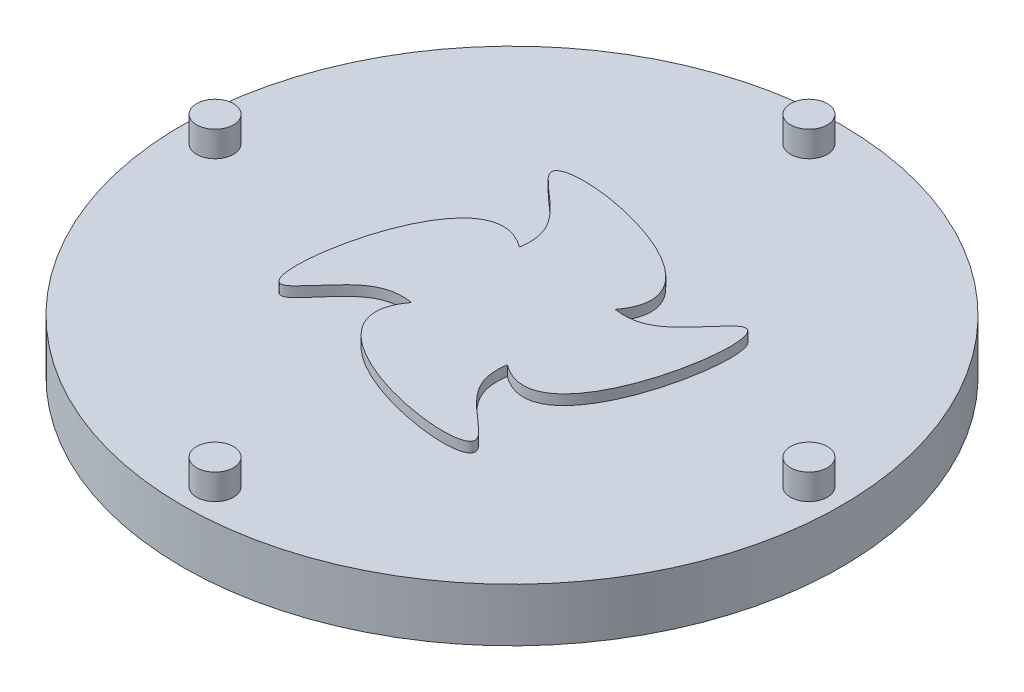
SolidWorks part; units mm, degrees
ref_plane "Alzado" through (0, 0, 0) normal (0, 0, 1) x (1, 0, 0)
ref_plane "Planta" through (0, 0, 0) normal (0, 1, 0) x (1, 0, 0)
ref_plane "Vista lateral" through (0, 0, 0) normal (1, 0, 0) x (0, 0, -1)
sketch "Croquis1" plane through (0, 0, 0) normal (0, 1, 0) x (1, 0, 0)
  circle A0 centre (0, 0) radius 61.815
  dimension "D1" = 123.63
extrude "Saliente-Extruir1" add sketch "Croquis1" along normal blind 10
sketch "Croquis2" plane through (0, 10, 0) normal (0, 1, 0) x (1, 0, 0)
  circle A0 centre (0, 55.6983) radius 3.45
  circle A1 centre (55.6983, 0) radius 3.45
  circle A2 centre (0, -55.6983) radius 3.45
  circle A3 centre (-55.6983, 0) radius 3.45
  point P12 (0, 0)
  dimension "D1" = 6.9
  dimension "D2" = 55.6983
  dimension "D3" = 4
extrude "Saliente-Extruir2" add sketch "Croquis2" along normal blind 4.8
sketch "Croquis3" plane through (0, 10, 0) normal (0, 1, 0) x (1, 0, 0)
  arc A0 (-8.7616, -8.3397) -> (-7.4839, -9.6174) centre (0.693, -0.1628) ccw
  spline S0 degree 3 poles (-9.4181, 8.8286) (-14.2169, 15.2422) (-2.4097, 26.5738) (27.3699, 28.459) (10.0048, 18.1784) (9.3364, 12.083) (9.6844, 9.9482) knots 0.00619 0.00619 0.00619 0.00619 0.153841 0.345958 0.455748 0.513421 0.513421 0.513421 0.513421
  spline S1 degree 3 poles (9.6844, 9.9482) (16.098, 14.7471) (27.4296, 2.9398) (29.3148, -26.8397) (19.0342, -9.4746) (12.9388, -8.8062) (10.804, -9.1542) knots 0.00619 0.00619 0.00619 0.00619 0.153841 0.345958 0.455748 0.513421 0.513421 0.513421 0.513421
  spline S2 degree 3 poles (10.804, -9.1542) (15.6028, -15.5678) (3.7956, -26.8994) (-25.9839, -28.7846) (-8.6188, -18.5041) (-7.9504, -12.4086) (-8.2984, -10.2739) knots 0.00619 0.00619 0.00619 0.00619 0.153841 0.345958 0.455748 0.513421 0.513421 0.513421 0.513421
  spline S3 degree 3 poles (-8.2984, -10.2739) (-14.712, -15.0727) (-26.0436, -3.2655) (-27.9289, 26.5141) (-17.6483, 9.149) (-11.5528, 8.4806) (-9.4181, 8.8286) knots 0.00619 0.00619 0.00619 0.00619 0.153841 0.345958 0.455748 0.513421 0.513421 0.513421 0.513421
  point P19 (0.693, -0.1628)
  dimension "D1" = 25
sketch "Croquis4" plane through (0, 0, 0) normal (0, -1, 0) x (1, 0, 0)
  spline S0 degree 3 poles (-9.5856, 9.2541) (-14.3844, 15.6677) (-2.5772, 26.9994) (27.2024, 28.8846) (9.8372, 18.604) (9.1688, 12.5086) (9.5168, 10.3738) knots 0.00619 0.00619 0.00619 0.00619 0.153841 0.345958 0.455748 0.513421 0.513421 0.513421 0.513421
  spline S1 degree 3 poles (9.5168, 10.3738) (15.9305, 15.1726) (27.2621, 3.3654) (29.1473, -26.4142) (18.8667, -9.049) (12.7713, -8.3807) (10.6365, -8.7286) knots 0.00619 0.00619 0.00619 0.00619 0.153841 0.345958 0.455748 0.513421 0.513421 0.513421 0.513421
  spline S2 degree 3 poles (10.6365, -8.7286) (15.4353, -15.1423) (3.6281, -26.4739) (-26.1514, -28.3591) (-8.7863, -18.0785) (-8.1179, -11.9831) (-8.4659, -9.8483) knots 0.00619 0.00619 0.00619 0.00619 0.153841 0.345958 0.455748 0.513421 0.513421 0.513421 0.513421
  spline S3 degree 3 poles (-8.4659, -9.8483) (-14.8795, -14.6471) (-26.2112, -2.8399) (-28.0964, 26.9396) (-17.8158, 9.5745) (-11.7204, 8.9061) (-9.5856, 9.2541) knots 0.00619 0.00619 0.00619 0.00619 0.153841 0.345958 0.455748 0.513421 0.513421 0.513421 0.513421
extrude "Saliente-Extruir5" add sketch "Croquis4" against normal blind 11.9
sketch "Croquis5" plane through (0, 0, 0) normal (0, -1, 0) x (1, 0, 0)
  line L0 (0, -967.0228) -> (0, -35.5) construction
  line L1 (-2.8962, 35.3817) -> (-2.8962, 36.3478)
  line L2 (12.1702, 43.8511) -> (10.4606, 44.29)
  line L3 (0.8825, 45.5) -> (-0.8825, 45.5)
  line L4 (2.8962, 35.3817) -> (2.8962, 36.3478)
  line L5 (22.6931, 39.4468) -> (21.1464, 40.2971)
  line L6 (31.7902, 32.564) -> (30.5036, 33.7722)
  line L7 (38.8898, 23.635) -> (37.9441, 25.1252)
  line L8 (43.5458, 13.221) -> (43.0004, 14.8996)
  line L9 (45.4656, 1.9762) -> (45.3548, 3.7377)
  line L10 (44.5287, -9.3927) -> (44.8594, -7.659)
  line L11 (40.7939, -20.1715) -> (41.5454, -18.5744)
  line L12 (34.4958, -29.6828) -> (35.6209, -28.3228)
  line L13 (26.0303, -37.329) -> (27.4582, -36.2915)
  line L14 (15.9291, -42.6297) -> (17.5702, -41.98)
  line L15 (4.8271, -45.2518) -> (6.5782, -45.0306)
  line L16 (-6.5782, -45.0306) -> (-4.8271, -45.2518)
  line L17 (-17.5702, -41.98) -> (-15.9291, -42.6297)
  line L18 (-27.4582, -36.2915) -> (-26.0303, -37.329)
  line L19 (-35.6209, -28.3228) -> (-34.4958, -29.6828)
  line L20 (-41.5454, -18.5744) -> (-40.7939, -20.1715)
  line L21 (-44.8594, -7.659) -> (-44.5287, -9.3927)
  line L22 (-45.3548, 3.7377) -> (-45.4656, 1.9762)
  line L23 (-43.0004, 14.8996) -> (-43.5458, 13.221)
  line L24 (-37.9441, 25.1252) -> (-38.8898, 23.635)
  line L25 (-30.5036, 33.7722) -> (-31.7902, 32.564)
  line L26 (-21.1464, 40.2971) -> (-22.6931, 39.4468)
  line L27 (-10.4606, 44.29) -> (-12.1702, 43.8511)
  line L28 (5.9939, 34.9903) -> (6.2341, 35.9262)
  line L29 (11.6043, 33.5498) -> (11.8445, 34.4857)
  line L30 (14.5073, 32.4004) -> (14.9728, 33.2471)
  line L31 (19.5832, 29.6099) -> (20.0487, 30.4566)
  line L32 (22.1092, 27.7747) -> (22.7706, 28.479)
  line L33 (26.3316, 23.8095) -> (26.993, 24.5139)
  line L34 (28.3219, 21.4038) -> (29.1376, 21.9215)
  line L35 (31.4256, 16.5131) -> (32.2414, 17.0308)
  line L36 (32.755, 13.688) -> (33.6739, 13.9865)
  line L37 (34.5449, 8.1791) -> (35.4638, 8.4777)
  line L38 (35.13, 5.1121) -> (36.0943, 5.1728)
  line L39 (35.4937, -0.6688) -> (36.458, -0.6082)
  line L40 (35.2976, -3.785) -> (36.2467, -3.966)
  line L41 (34.2123, -9.4748) -> (35.1613, -9.6558)
  line L42 (33.2474, -12.4442) -> (34.1217, -12.8556)
  line L43 (30.7811, -17.6853) -> (31.6554, -18.0967)
  line L44 (29.1081, -20.3216) -> (29.8526, -20.9374)
  line L45 (25.4159, -24.7847) -> (26.1604, -25.4005)
  line L46 (23.1399, -26.922) -> (23.7078, -27.7037)
  line L47 (18.4538, -30.3267) -> (19.0217, -31.1084)
  line L48 (15.7177, -31.8309) -> (16.0733, -32.7292)
  line L49 (10.3321, -33.9632) -> (10.6877, -34.8615)
  line L50 (7.3078, -34.7397) -> (7.4289, -35.6982)
  line L51 (1.5611, -35.4657) -> (1.6822, -36.4242)
  line L52 (-1.5611, -35.4657) -> (-1.6822, -36.4242)
  line L53 (-7.3078, -34.7397) -> (-7.4289, -35.6982)
  line L54 (-10.3321, -33.9632) -> (-10.6877, -34.8615)
  line L55 (-15.7177, -31.8309) -> (-16.0733, -32.7292)
  line L56 (-18.4538, -30.3267) -> (-19.0217, -31.1084)
  line L57 (-23.1399, -26.922) -> (-23.7078, -27.7037)
  line L58 (-25.4159, -24.7847) -> (-26.1604, -25.4005)
  line L59 (-29.1081, -20.3216) -> (-29.8526, -20.9374)
  line L60 (-30.7811, -17.6853) -> (-31.6554, -18.0967)
  line L61 (-33.2474, -12.4442) -> (-34.1217, -12.8556)
  line L62 (-34.2123, -9.4748) -> (-35.1613, -9.6558)
  line L63 (-35.2976, -3.785) -> (-36.2467, -3.966)
  line L64 (-35.4937, -0.6688) -> (-36.458, -0.6082)
  line L65 (-35.13, 5.1121) -> (-36.0943, 5.1728)
  line L66 (-34.5449, 8.1791) -> (-35.4638, 8.4777)
  line L67 (-32.755, 13.688) -> (-33.6739, 13.9865)
  line L68 (-31.4256, 16.5131) -> (-32.2414, 17.0308)
  line L69 (-28.3219, 21.4038) -> (-29.1376, 21.9215)
  line L70 (-26.3316, 23.8095) -> (-26.993, 24.5139)
  line L71 (-22.1092, 27.7747) -> (-22.7706, 28.479)
  line L72 (-19.5832, 29.6099) -> (-20.0487, 30.4566)
  line L73 (-14.5073, 32.4004) -> (-14.9728, 33.2471)
  line L74 (-11.6043, 33.5498) -> (-11.8445, 34.4857)
  line L75 (-5.9939, 34.9903) -> (-6.2341, 35.9262)
  arc A0 (-2.8962, 35.3817) -> (-5.9939, 34.9903) centre (0, 0) ccw
  arc A1 (-2.8962, 36.3478) -> (-0.8825, 45.5) centre (18.9088, 36.3478) cw
  arc A2 (2.8962, 36.3478) -> (0.8825, 45.5) centre (-18.9088, 36.3478) ccw
  arc A3 (6.2341, 35.9262) -> (10.4606, 44.29) centre (27.3541, 30.5035) cw
  arc A4 (14.9728, 33.2471) -> (21.1464, 40.2971) centre (34.0806, 22.7425) cw
  arc A5 (22.7706, 28.479) -> (30.5036, 33.7722) centre (38.6658, 13.5524) cw
  arc A6 (29.1376, 21.9215) -> (37.9441, 25.1252) centre (40.8214, 3.5109) cw
  arc A7 (33.6739, 13.9865) -> (43.0004, 14.8996) centre (40.412, -6.7513) cw
  arc A8 (36.0943, 5.1728) -> (45.3548, 3.7377) centre (37.4634, -16.5892) cw
  arc A9 (36.2467, -3.966) -> (44.8594, -7.659) centre (32.1609, -25.3848) cw
  arc A10 (34.1217, -12.8556) -> (41.5454, -18.5744) centre (24.8375, -32.5854) cw
  arc A11 (29.8526, -20.9374) -> (35.6209, -28.3228) centre (15.9535, -37.7385) cw
  arc A12 (23.7078, -27.7037) -> (27.4582, -36.2915) centre (6.0672, -40.5204) cw
  arc A13 (16.0733, -32.7292) -> (17.5702, -41.98) centre (-4.2005, -40.7562) cw
  arc A14 (7.4289, -35.6982) -> (6.5782, -45.0306) centre (-14.2041, -38.4311) cw
  arc A15 (-1.6822, -36.4242) -> (-4.8271, -45.2518) centre (-23.3153, -33.6913) cw
  arc A16 (-10.6877, -34.8615) -> (-15.9291, -42.6297) centre (-30.9615, -26.8346) cw
  arc A17 (-19.0217, -31.1084) -> (-26.0303, -37.329) centre (-36.6623, -18.2917) cw
  arc A18 (-26.1604, -25.4005) -> (-34.4958, -29.6828) centre (-40.0594, -8.5995) cw
  arc A19 (-31.6554, -18.0967) -> (-40.7939, -20.1715) centre (-40.9395, 1.6331) cw
  arc A20 (-35.1613, -9.6558) -> (-44.5287, -9.3927) centre (-39.2472, 11.763) cw
  arc A21 (-36.458, -0.6082) -> (-45.4656, 1.9762) centre (-35.0888, 21.1538) cw
  arc A22 (-35.4638, 8.4777) -> (-43.5458, 13.221) centre (-28.7257, 29.2155) cw
  arc A23 (-32.2414, 17.0308) -> (-38.8898, 23.635) centre (-20.5576, 35.4414) cw
  arc A24 (-26.993, 24.5139) -> (-31.7902, 32.564) centre (-11.0979, 39.4404) cw
  arc A25 (-20.0487, 30.4566) -> (-22.6931, 39.4468) centre (-0.9408, 40.9613) cw
  arc A26 (-11.8445, 34.4857) -> (-12.1702, 43.8511) centre (9.2754, 39.9083) cw
  arc A27 (11.8445, 34.4857) -> (12.1702, 43.8511) centre (-9.2754, 39.9083) ccw
  arc A28 (20.0487, 30.4566) -> (22.6931, 39.4468) centre (0.9408, 40.9613) ccw
  arc A29 (26.993, 24.5139) -> (31.7902, 32.564) centre (11.0979, 39.4404) ccw
  arc A30 (32.2414, 17.0308) -> (38.8898, 23.635) centre (20.5576, 35.4414) ccw
  arc A31 (35.4638, 8.4777) -> (43.5458, 13.221) centre (28.7257, 29.2155) ccw
  arc A32 (36.458, -0.6082) -> (45.4656, 1.9762) centre (35.0888, 21.1538) ccw
  arc A33 (35.1613, -9.6558) -> (44.5287, -9.3927) centre (39.2472, 11.763) ccw
  arc A34 (31.6554, -18.0967) -> (40.7939, -20.1715) centre (40.9395, 1.6331) ccw
  arc A35 (26.1604, -25.4005) -> (34.4958, -29.6828) centre (40.0594, -8.5995) ccw
  arc A36 (19.0217, -31.1084) -> (26.0303, -37.329) centre (36.6623, -18.2917) ccw
  arc A37 (10.6877, -34.8615) -> (15.9291, -42.6297) centre (30.9615, -26.8346) ccw
  arc A38 (1.6822, -36.4242) -> (4.8271, -45.2518) centre (23.3153, -33.6913) ccw
  arc A39 (-7.4289, -35.6982) -> (-6.5782, -45.0306) centre (14.2041, -38.4311) ccw
  arc A40 (-16.0733, -32.7292) -> (-17.5702, -41.98) centre (4.2005, -40.7562) ccw
  arc A41 (-23.7078, -27.7037) -> (-27.4582, -36.2915) centre (-6.0672, -40.5204) ccw
  arc A42 (-29.8526, -20.9374) -> (-35.6209, -28.3228) centre (-15.9535, -37.7385) ccw
  arc A43 (-34.1217, -12.8556) -> (-41.5454, -18.5744) centre (-24.8375, -32.5854) ccw
  arc A44 (-36.2467, -3.966) -> (-44.8594, -7.659) centre (-32.1609, -25.3848) ccw
  arc A45 (-36.0943, 5.1728) -> (-45.3548, 3.7377) centre (-37.4634, -16.5892) ccw
  arc A46 (-33.6739, 13.9865) -> (-43.0004, 14.8996) centre (-40.412, -6.7513) ccw
  arc A47 (-29.1376, 21.9215) -> (-37.9441, 25.1252) centre (-40.8214, 3.5109) ccw
  arc A48 (-22.7706, 28.479) -> (-30.5036, 33.7722) centre (-38.6658, 13.5524) ccw
  arc A49 (-14.9728, 33.2471) -> (-21.1464, 40.2971) centre (-34.0806, 22.7425) ccw
  arc A50 (-6.2341, 35.9262) -> (-10.4606, 44.29) centre (-27.3541, 30.5035) ccw
  arc A51 (5.9939, 34.9903) -> (2.8962, 35.3817) centre (0, 0) ccw
  arc A52 (-11.6043, 33.5498) -> (-14.5073, 32.4004) centre (0, 0) ccw
  arc A53 (-19.5832, 29.6099) -> (-22.1092, 27.7747) centre (0, 0) ccw
  arc A54 (-26.3316, 23.8095) -> (-28.3219, 21.4038) centre (0, 0) ccw
  arc A55 (22.1092, 27.7747) -> (19.5832, 29.6099) centre (0, 0) ccw
  arc A56 (28.3219, 21.4038) -> (26.3316, 23.8095) centre (0, 0) ccw
  arc A57 (32.755, 13.688) -> (31.4256, 16.5131) centre (0, 0) ccw
  arc A58 (35.13, 5.1121) -> (34.5449, 8.1791) centre (0, 0) ccw
  arc A59 (35.2976, -3.785) -> (35.4937, -0.6688) centre (0, 0) ccw
  arc A60 (33.2474, -12.4442) -> (34.2123, -9.4748) centre (0, 0) ccw
  arc A61 (-31.4256, 16.5131) -> (-32.755, 13.688) centre (0, 0) ccw
  arc A62 (-34.5449, 8.1791) -> (-35.13, 5.1121) centre (0, 0) ccw
  arc A63 (-35.4937, -0.6688) -> (-35.2976, -3.785) centre (0, 0) ccw
  arc A64 (-34.2123, -9.4748) -> (-33.2474, -12.4442) centre (0, 0) ccw
  arc A65 (-30.7811, -17.6853) -> (-29.1081, -20.3216) centre (0, 0) ccw
  arc A66 (-25.4159, -24.7847) -> (-23.1399, -26.922) centre (0, 0) ccw
  arc A67 (-18.4538, -30.3267) -> (-15.7177, -31.8309) centre (0, 0) ccw
  arc A68 (-10.3321, -33.9632) -> (-7.3078, -34.7397) centre (0, 0) ccw
  arc A69 (7.3078, -34.7397) -> (10.3321, -33.9632) centre (0, 0) ccw
  arc A70 (-1.5611, -35.4657) -> (1.5611, -35.4657) centre (0, 0) ccw
  arc A71 (15.7177, -31.8309) -> (18.4538, -30.3267) centre (0, 0) ccw
  arc A72 (23.1399, -26.922) -> (25.4159, -24.7847) centre (0, 0) ccw
  arc A73 (29.1081, -20.3216) -> (30.7811, -17.6853) centre (0, 0) ccw
  arc A74 (14.5073, 32.4004) -> (11.6043, 33.5498) centre (0, 0) ccw
  point P11 (0, 42)
  point P88 (0, 0)
  point P185 (0, 0)
  point P259 (0, 0)
  dimension "D1" = 71
  dimension "D2" = 25
  dimension "D3" = 25
  dimension "D4" = 25
extrude "Cortar-Extruir1" cut sketch "Croquis5" against normal blind 3
